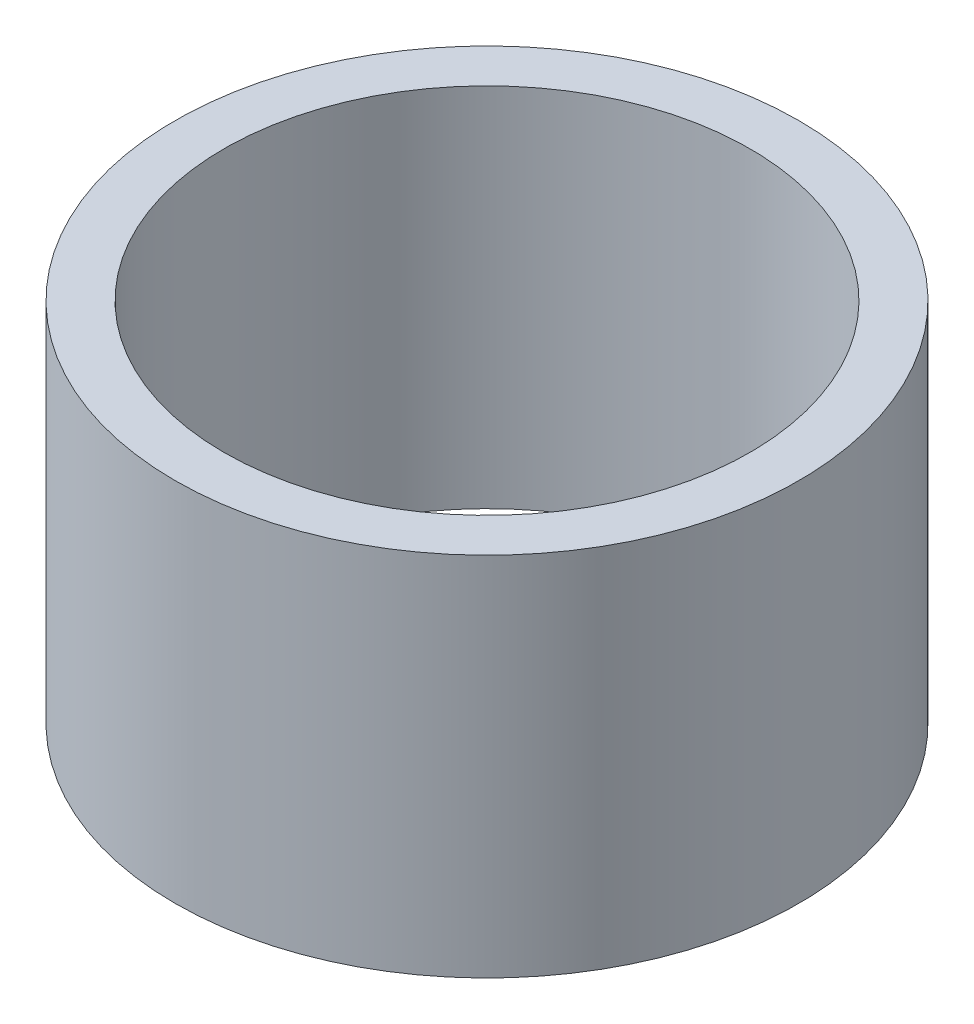
SolidWorks part; units mm, degrees
ref_plane "Front Plane" through (0, 0, 0) normal (0, 0, 1) x (1, 0, 0)
ref_plane "Top Plane" through (0, 0, 0) normal (0, 1, 0) x (1, 0, 0)
ref_plane "Right Plane" through (0, 0, 0) normal (1, 0, 0) x (0, 0, -1)
sketch "Sketch1" plane through (0, 0, 0) normal (0, 1, 0) x (1, 0, 0)
  circle A0 centre (0, 0) radius 27.3685
  circle A1 centre (0, 0) radius 32.4485
  dimension "D1" = 54.737
  dimension "D2" = 5.08
extrude "Boss-Extrude1" add sketch "Sketch1" along normal blind 38.1
